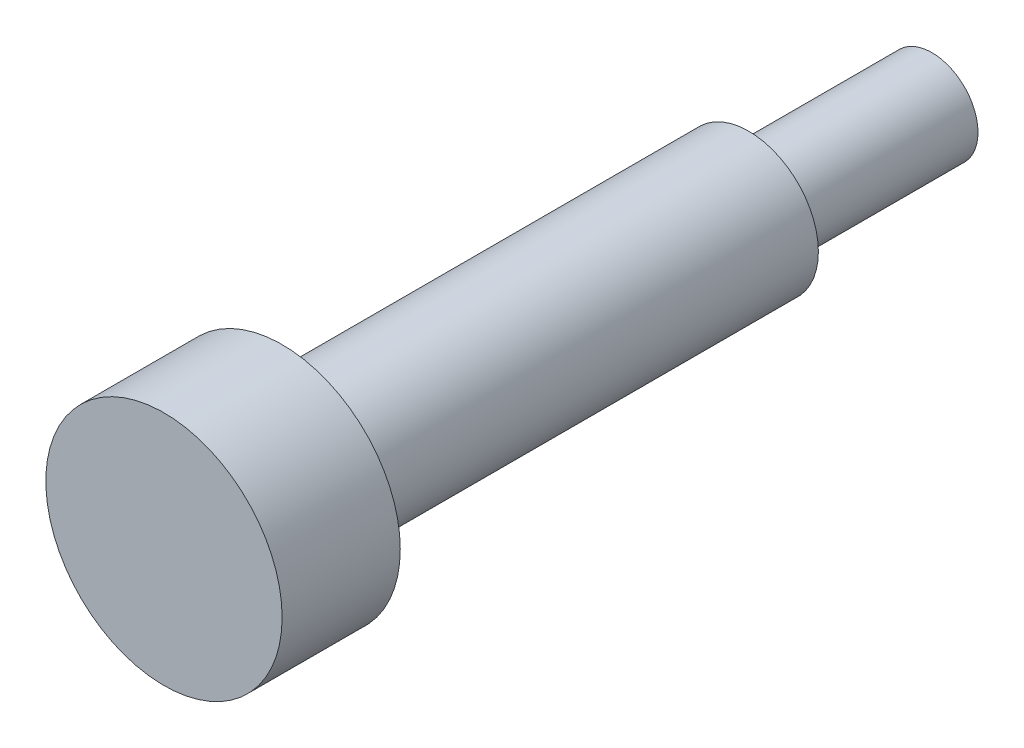
SolidWorks part; units mm, degrees
material "ABS"
ref_plane "Front Plane" through (0, 0, 0) normal (0, 0, 1) x (1, 0, 0)
ref_plane "Top Plane" through (0, 0, 0) normal (0, 1, 0) x (1, 0, 0)
ref_plane "Right Plane" through (0, 0, 0) normal (1, 0, 0) x (0, 0, -1)
sketch "Sketch1" plane through (0, 0, 0) normal (0, 0, 1) x (1, 0, 0)
  circle A0 centre (0, 0) radius 1.143
  circle A1 centre (0, 0) radius 1.9808
extrude "Boss-Extrude1" add sketch "Sketch1" along normal blind 7.874 contours A1
sketch "Sketch2" plane through (0, 0, 0) normal (0, 0, -1) x (-1, 0, 0)
  circle A3 centre (0, 0) radius 1.143
  circle A4 centre (0, 0) radius 1.143
  dimension "D2" = 0
extrude "Cut-Extrude2" cut sketch "Sketch2" against normal through all
sketch "Sketch3" plane through (0, 0, 7.874) normal (0, 0, 1) x (1, 0, 0)
  circle A0 centre (0, 0) radius 2.9915
extrude "Boss-Extrude2" add sketch "Sketch3" along normal blind 20.066
sketch "Sketch4" plane through (0, 0, 27.94) normal (0, 0, 1) x (1, 0, 0)
  circle A0 centre (0, 0) radius 5.08
extrude "Boss-Extrude3" add sketch "Sketch4" along normal blind 5.08
